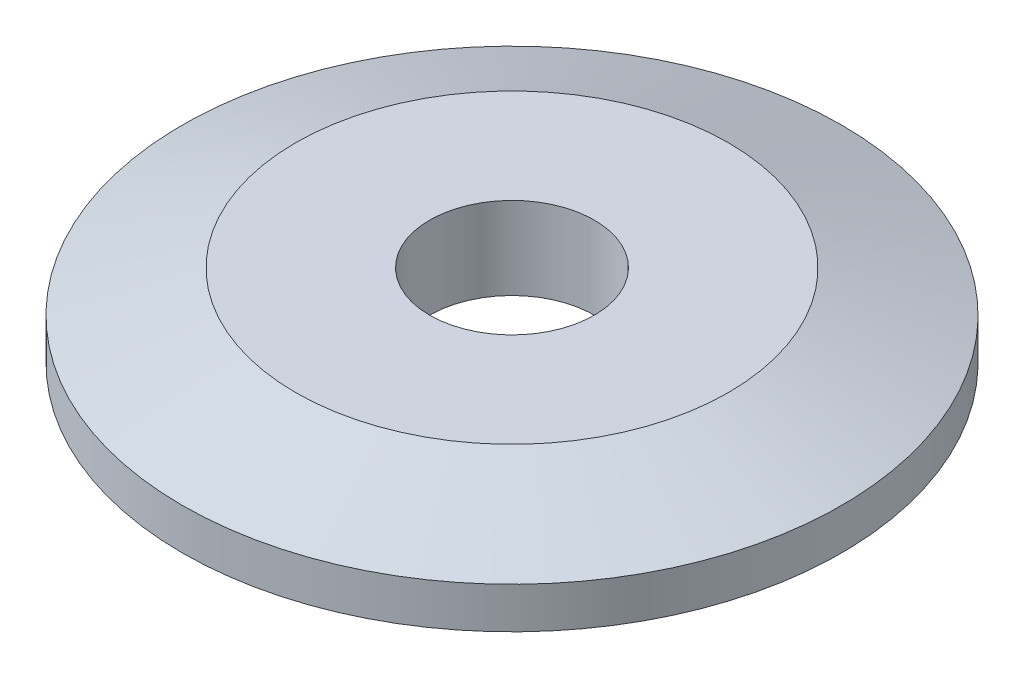
SolidWorks part; units mm, degrees
ref_plane "Front Plane" through (0, 0, 0) normal (0, 0, 1) x (1, 0, 0)
ref_plane "Top Plane" through (0, 0, 0) normal (0, 1, 0) x (1, 0, 0)
ref_plane "Right Plane" through (0, 0, 0) normal (1, 0, 0) x (0, 0, -1)
sketch "Sketch1" plane through (0, 0, 0) normal (0, 1, 0) x (1, 0, 0)
  circle A0 centre (0, 0) radius 8
  dimension "D1" = 16
extrude "Boss-Extrude1" add sketch "Sketch1" along normal blind 2
chamfer "Chamfer1" distance 1 angle 70 1 edges at (0, 2, 8)
sketch "Sketch2" plane through (0, 2, 0) normal (0, 1, 0) x (1, 0, 0)
  circle A0 centre (0, 0) radius 2
  dimension "D1" = 4
extrude "Cut-Extrude1" cut sketch "Sketch2" against normal through all
